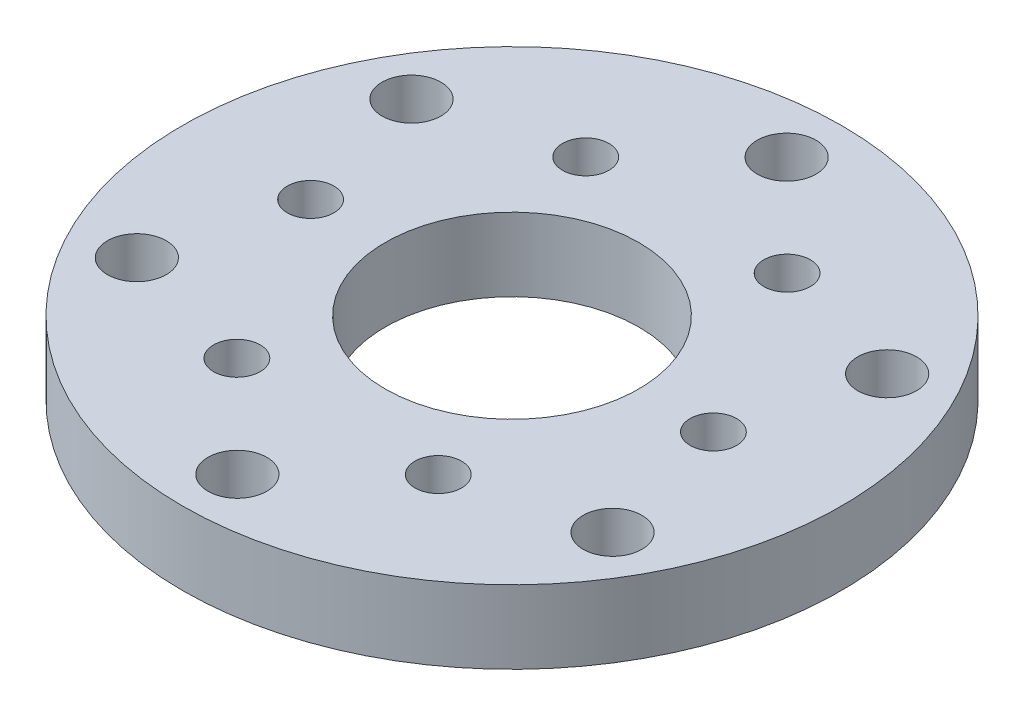
SolidWorks part; units mm, degrees
material "6061-T6 (SS)"
ref_plane "Front Plane" through (0, 0, 0) normal (0, 0, 1) x (1, 0, 0)
ref_plane "Top Plane" through (0, 0, 0) normal (0, 1, 0) x (1, 0, 0)
ref_plane "Right Plane" through (0, 0, 0) normal (1, 0, 0) x (0, 0, -1)
sketch "Sketch1" plane through (0, 0, 0) normal (0, 1, 0) x (1, 0, 0)
  circle A0 centre (0, 0) radius 28.575
  dimension "D1" = 57.15
extrude "Boss-Extrude1" add sketch "Sketch1" along normal blind 6.35
hole_wizard "1/4-20 Tapped Hole1" positions "Sketch3" profile "Sketch4" tap size "1/4-20" standard "ANSI Inch" end condition through all
sketch "Sketch3" plane through (0, 6.35, 0) normal (0, 1, 0) x (1, 0, 0)
  line L0 (0, 0) -> (0, 23.8125) construction
  circle A0 centre (0, 0) radius 23.8125
  point P0 (0, 23.8125)
  point P22 (20.6222, 11.9063)
  point P23 (20.6222, -11.9062)
  point P24 (0, -23.8125)
  point P25 (-20.6222, -11.9063)
  point P26 (-20.6222, 11.9062)
  dimension "D1" = 47.625
  dimension "D2" = 6
sketch "Sketch4" plane through (0, 6.35, -23.8125) normal (1, 0, 0) x (0, 0, 1)
  line L0 (0, 0) -> (0, 6.35)
  line L1 (0, 6.35) -> (2.5527, 6.35)
  line L2 (2.5527, 6.35) -> (2.5527, 0)
  line L5 (2.5527, 0) -> (0, 0)
  line L11 (0, -6.35) -> (0, 107.95) construction
  dimension "Thru Tap Drill Dia." = 5.1054
  dimension "Thru Tap Drill Depth" = 6.35
cosmetic thread "Hole Thread1"
cosmetic thread "Hole Thread2"
cosmetic thread "Hole Thread3"
cosmetic thread "Hole Thread4"
cosmetic thread "Hole Thread5"
cosmetic thread "Hole Thread6"
sketch "Sketch5" plane through (0, 6.35, 0) normal (0, 1, 0) x (1, 0, 0)
  circle A0 centre (0, 0) radius 11
  dimension "D1" = 22
extrude "Cut-Extrude1" cut sketch "Sketch5" against normal through all
hole_wizard "#10-32 Tapped Hole1" positions "Sketch7" profile "Sketch8" tap size "#10-32" standard "ANSI Inch" end condition through all
sketch "Sketch7" plane through (0, 6.35, 0) normal (0, 1, 0) x (1, 0, 0)
  line L0 (0, 0) -> (-8.7313, 15.123) construction
  line L2 (0, 0) -> (0, 17.4625) construction
  circle A0 centre (0, 0) radius 17.4625
  point P0 (-8.7313, 15.123)
  point P22 (8.7312, 15.123)
  point P23 (17.4625, 0)
  point P24 (8.7313, -15.123)
  point P25 (-8.7312, -15.123)
  point P26 (-17.4625, 0)
  dimension "D1" = 34.925
  dimension "D2" = 30
  dimension "D3" = 6
sketch "Sketch8" plane through (-8.7313, 6.35, -15.123) normal (1, 0, 0) x (0, 0, 1)
  line L0 (0, 0) -> (0, 6.35)
  line L1 (0, 6.35) -> (2.0193, 6.35)
  line L2 (2.0193, 6.35) -> (2.0193, 0)
  line L5 (2.0193, 0) -> (0, 0)
  line L11 (0, -6.35) -> (0, 107.95) construction
  dimension "Thru Tap Drill Dia." = 4.0386
  dimension "Thru Tap Drill Depth" = 6.35
cosmetic thread "Hole Thread7"
cosmetic thread "Hole Thread8"
cosmetic thread "Hole Thread9"
cosmetic thread "Hole Thread10"
cosmetic thread "Hole Thread11"
cosmetic thread "Hole Thread12"
